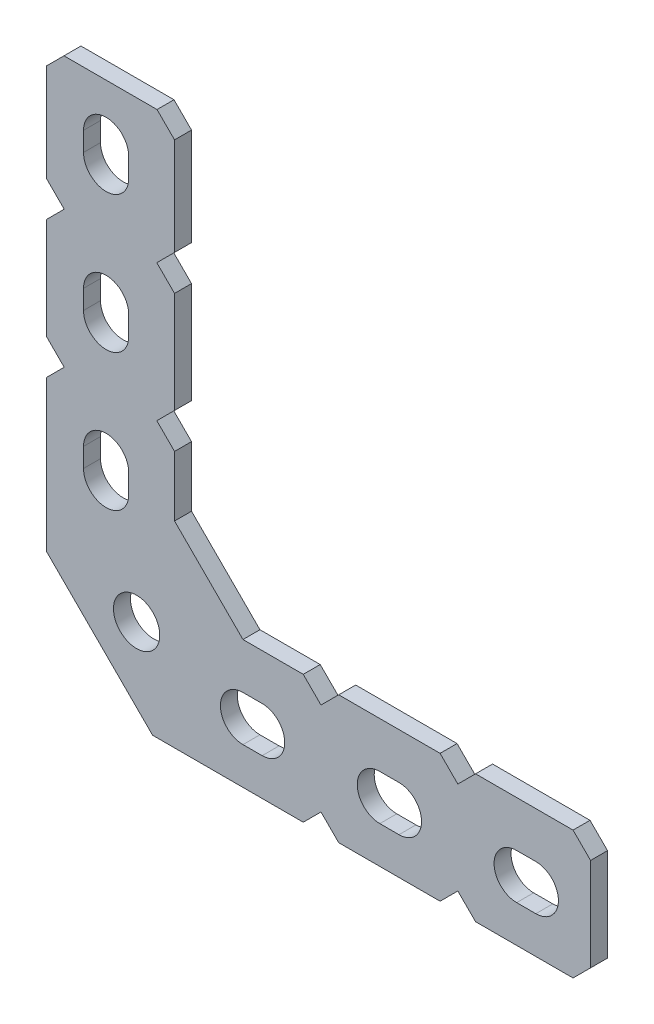
SolidWorks part; units mm, degrees
material "Custom Plastic"
ref_plane "Front Plane" through (0, 0, 0) normal (0, 0, 1) x (1, 0, 0)
ref_plane "Top Plane" through (0, 0, 0) normal (0, 1, 0) x (1, 0, 0)
ref_plane "Right Plane" through (0, 0, 0) normal (1, 0, 0) x (0, 0, -1)
ref_plane "Plane1" through (0, 0, 1.5748) normal (0, 0, 1) x (1, 0, 0)
sketch "Sketch1" plane through (0, 0, 1.5748) normal (0, 0, 1) x (1, 0, 0)
  line L0 (6.35, 34.285) -> (6.35, 43.3324)
  line L1 (6.35, 43.3324) -> (4.7244, 44.958)
  line L2 (4.7244, 44.958) -> (-3.9116, 44.958)
  line L3 (-3.9116, 44.958) -> (-5.5372, 43.3324)
  line L4 (-5.5372, 43.3324) -> (-5.5372, 34.285)
  line L5 (-5.5372, 34.285) -> (-3.8912, 32.639)
  line L6 (-3.8912, 32.639) -> (-5.5372, 30.993)
  line L7 (-5.5372, 30.993) -> (-5.5372, 21.585)
  line L8 (-5.5372, 21.585) -> (-3.8912, 19.939)
  line L9 (-3.8912, 19.939) -> (-5.5372, 18.293)
  line L10 (-5.5372, 18.293) -> (-5.5372, 4.3134)
  line L11 (-5.5372, 4.3134) -> (4.3134, -5.5372)
  line L12 (4.3134, -5.5372) -> (18.293, -5.5372)
  line L13 (18.293, -5.5372) -> (19.939, -3.8912)
  line L14 (19.939, -3.8912) -> (21.585, -5.5372)
  line L15 (21.585, -5.5372) -> (30.993, -5.5372)
  line L16 (30.993, -5.5372) -> (32.639, -3.8912)
  line L17 (32.639, -3.8912) -> (34.285, -5.5372)
  line L18 (34.285, -5.5372) -> (43.3324, -5.5372)
  line L19 (43.3324, -5.5372) -> (44.958, -3.9116)
  line L20 (44.958, -3.9116) -> (44.958, 4.7244)
  line L21 (44.958, 4.7244) -> (43.3324, 6.35)
  line L22 (43.3324, 6.35) -> (34.285, 6.35)
  line L23 (34.285, 6.35) -> (32.639, 4.704)
  line L24 (32.639, 4.704) -> (30.993, 6.35)
  line L25 (30.993, 6.35) -> (21.585, 6.35)
  line L26 (21.585, 6.35) -> (19.939, 4.704)
  line L27 (19.939, 4.704) -> (18.293, 6.35)
  line L28 (18.293, 6.35) -> (12.7, 6.35)
  line L29 (12.7, 6.35) -> (6.35, 12.7)
  line L30 (6.35, 12.7) -> (6.35, 18.293)
  line L31 (6.35, 18.293) -> (4.704, 19.939)
  line L32 (4.704, 19.939) -> (6.35, 21.585)
  line L33 (6.35, 21.585) -> (6.35, 30.993)
  line L34 (6.35, 30.993) -> (4.704, 32.639)
  line L35 (4.704, 32.639) -> (6.35, 34.285)
  line L36 (12.7, 2.0955) -> (14.478, 2.0955)
  line L37 (14.478, -2.0955) -> (12.7, -2.0955)
  line L38 (-2.0955, 38.1) -> (-2.0955, 39.878)
  line L39 (2.0955, 39.878) -> (2.0955, 38.1)
  line L40 (-2.0955, 12.7) -> (-2.0955, 14.478)
  line L41 (2.0955, 14.478) -> (2.0955, 12.7)
  line L42 (-2.0955, 25.4) -> (-2.0955, 27.178)
  line L43 (2.0955, 27.178) -> (2.0955, 25.4)
  line L44 (25.4, 2.0955) -> (27.178, 2.0955)
  line L45 (27.178, -2.0955) -> (25.4, -2.0955)
  line L46 (38.1, 2.0955) -> (39.878, 2.0955)
  line L47 (39.878, -2.0955) -> (38.1, -2.0955)
  circle A0 centre (2.8288, 2.8288) radius 2.1463
  arc A1 (14.478, 2.0955) -> (14.478, -2.0955) centre (14.478, 0) cw
  arc A2 (12.7, -2.0955) -> (12.7, 2.0955) centre (12.7, 0) cw
  arc A3 (-2.0955, 39.878) -> (2.0955, 39.878) centre (0, 39.878) cw
  arc A4 (2.0955, 38.1) -> (-2.0955, 38.1) centre (0, 38.1) cw
  arc A5 (-2.0955, 14.478) -> (2.0955, 14.478) centre (0, 14.478) cw
  arc A6 (2.0955, 12.7) -> (-2.0955, 12.7) centre (0, 12.7) cw
  arc A7 (-2.0955, 27.178) -> (2.0955, 27.178) centre (0, 27.178) cw
  arc A8 (2.0955, 25.4) -> (-2.0955, 25.4) centre (0, 25.4) cw
  arc A9 (27.178, 2.0955) -> (27.178, -2.0955) centre (27.178, 0) cw
  arc A10 (25.4, -2.0955) -> (25.4, 2.0955) centre (25.4, 0) cw
  arc A11 (39.878, 2.0955) -> (39.878, -2.0955) centre (39.878, 0) cw
  arc A12 (38.1, -2.0955) -> (38.1, 2.0955) centre (38.1, 0) cw
extrude "Boss-Extrude1" add sketch "Sketch1" against normal blind 1.5748
